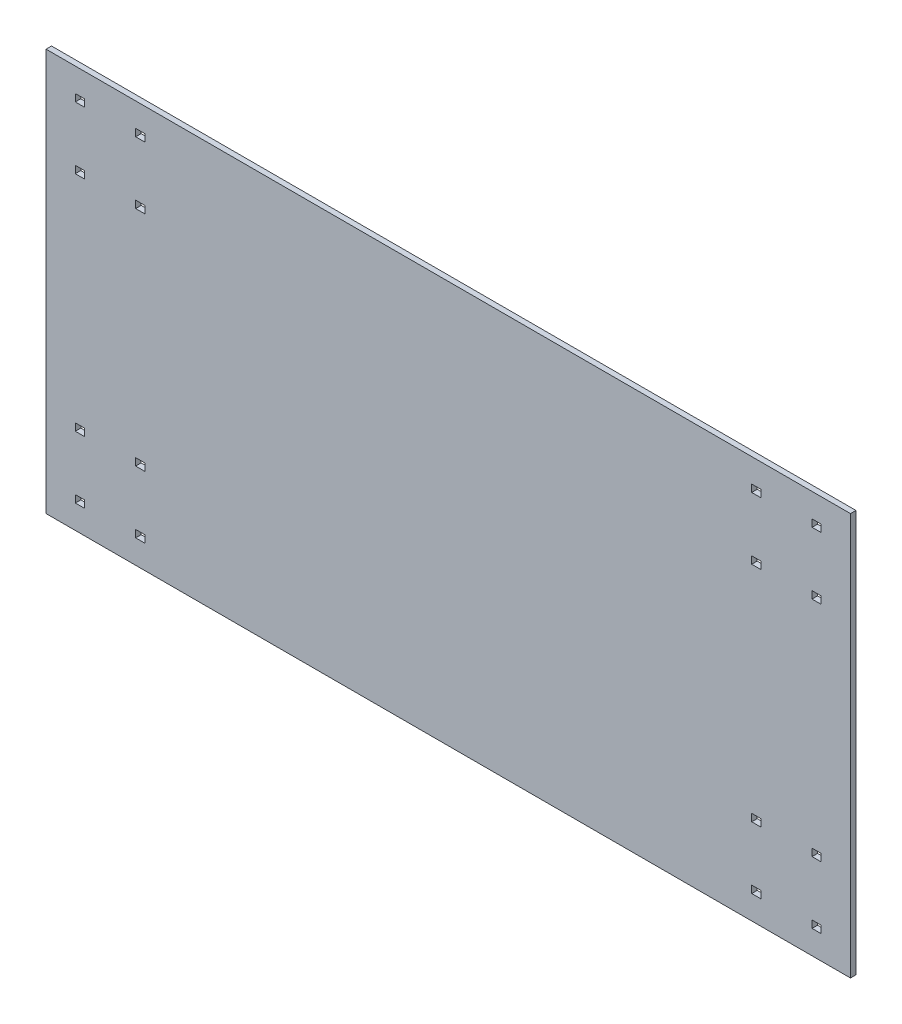
SolidWorks part; units mm, degrees
ref_plane "Plan de face" through (0, 0, 0) normal (0, 0, 1) x (1, 0, 0)
ref_plane "Plan de dessus" through (0, 0, 0) normal (0, 1, 0) x (1, 0, 0)
ref_plane "Plan de droite" through (0, 0, 0) normal (1, 0, 0) x (0, 0, -1)
sketch "Esquisse1" plane through (0, 0, 0) normal (0, 0, 1) x (1, 0, 0)
  line L1 (-220, 110) -> (220, 110)
  line L2 (-220, 110) -> (-220, -110)
  line L3 (-220, -110) -> (220, -110)
  line L4 (220, 110) -> (220, -110)
  line L5 (-220, 110) -> (220, -110) construction
  line L6 (-220, -110) -> (220, 110) construction
  point P0 (0, 0)
  dimension "D1" = 440
  dimension "D2" = 220
extrude "Boss.-Extru.1" add sketch "Esquisse1" along normal blind 3
sketch "Esquisse2" plane through (0, 0, 0) normal (0, 0, -1) x (-1, 0, 0)
  line L0 (0, 110) -> (0, -110) construction
  line L1 (-220, 110) -> (220, 110) construction
  line L2 (220, -110) -> (-220, -110) construction
  line L3 (-220, 0) -> (220, 0) construction
  line L4 (-220, -110) -> (-220, 110) construction
  line L5 (220, 110) -> (220, -110) construction
  line L6 (-199, 95) -> (-171, 95) construction
  line L7 (-204, 97) -> (-199, 97)
  line L8 (-204, 97) -> (-204, 93)
  line L9 (-204, 93) -> (-199, 93)
  line L10 (-199, 97) -> (-199, 93)
  line L11 (-204, 97) -> (-199, 93) construction
  line L12 (-204, 93) -> (-199, 97) construction
  line L13 (-171, 97) -> (-166, 97)
  line L14 (-171, 97) -> (-171, 93)
  line L15 (-171, 93) -> (-166, 93)
  line L16 (-166, 97) -> (-166, 93)
  line L17 (-171, 97) -> (-166, 93) construction
  line L18 (-171, 93) -> (-166, 97) construction
  line L19 (-185, 94) -> (-185, 62) construction
  line L20 (-201, 78) -> (-169, 78) construction
  line L21 (-171, 63) -> (-166, 63)
  line L22 (-166, 59) -> (-166, 63)
  line L23 (-171, 59) -> (-166, 59)
  line L24 (-171, 59) -> (-171, 63)
  line L25 (-204, 59) -> (-199, 59)
  line L26 (-204, 59) -> (-204, 63)
  line L27 (-204, 63) -> (-199, 63)
  line L28 (-199, 59) -> (-199, 63)
  line L29 (171, 59) -> (171, 63)
  line L30 (171, 59) -> (166, 59)
  line L31 (166, 59) -> (166, 63)
  line L32 (171, 63) -> (166, 63)
  line L33 (199, 59) -> (199, 63)
  line L34 (204, 63) -> (199, 63)
  line L35 (204, 59) -> (204, 63)
  line L36 (204, 59) -> (199, 59)
  line L37 (166, 97) -> (166, 93)
  line L38 (171, 93) -> (166, 93)
  line L39 (171, 97) -> (166, 97)
  line L40 (171, 97) -> (171, 93)
  line L41 (204, 93) -> (199, 93)
  line L42 (199, 97) -> (199, 93)
  line L43 (204, 97) -> (199, 97)
  line L44 (204, 97) -> (204, 93)
  line L45 (-166, -97) -> (-166, -93)
  line L46 (-171, -93) -> (-166, -93)
  line L47 (-171, -97) -> (-171, -93)
  line L48 (-171, -97) -> (-166, -97)
  line L49 (-199, -97) -> (-199, -93)
  line L50 (-204, -93) -> (-199, -93)
  line L51 (-204, -97) -> (-199, -97)
  line L52 (-204, -97) -> (-204, -93)
  line L53 (171, -63) -> (166, -63)
  line L54 (166, -59) -> (166, -63)
  line L55 (171, -59) -> (166, -59)
  line L56 (171, -59) -> (171, -63)
  line L57 (204, -59) -> (199, -59)
  line L58 (204, -59) -> (204, -63)
  line L59 (204, -63) -> (199, -63)
  line L60 (199, -59) -> (199, -63)
  line L61 (204, -97) -> (204, -93)
  line L62 (204, -97) -> (199, -97)
  line L63 (199, -97) -> (199, -93)
  line L64 (204, -93) -> (199, -93)
  line L65 (171, -97) -> (171, -93)
  line L66 (171, -97) -> (166, -97)
  line L67 (171, -93) -> (166, -93)
  line L68 (166, -97) -> (166, -93)
  line L69 (-171, -59) -> (-171, -63)
  line L70 (-171, -59) -> (-166, -59)
  line L71 (-166, -59) -> (-166, -63)
  line L72 (-171, -63) -> (-166, -63)
  line L73 (-199, -59) -> (-199, -63)
  line L74 (-204, -63) -> (-199, -63)
  line L75 (-204, -59) -> (-204, -63)
  line L76 (-204, -59) -> (-199, -59)
  circle A0 centre (-185, 78) radius 16 construction
  point P20 (-201.5, 95)
  point P25 (-168.5, 95)
  dimension "D1" = 32
  dimension "D2" = 32
  dimension "D3" = 35
  dimension "D4" = 28
  dimension "D5" = 5
  dimension "D6" = 4
  dimension "D7" = 5
  dimension "D8" = 4
  dimension "D9" = 15
  dimension "D10" = 14
extrude "Enlèv. mat.-Extru.1" cut sketch "Esquisse2" against normal blind 3
